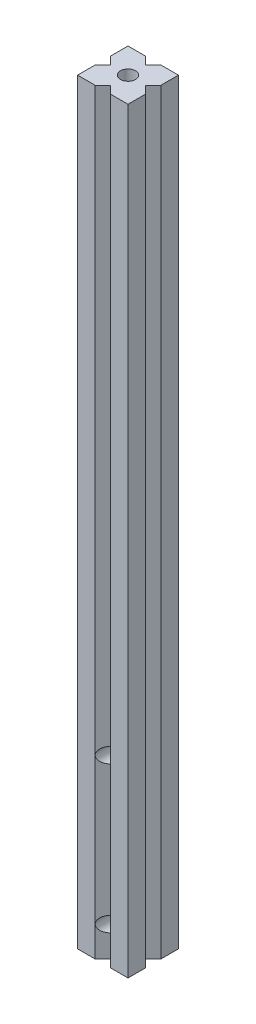
SolidWorks part; units mm, degrees
ref_plane "Front" through (0, 0, 0) normal (0, 0, 1) x (1, 0, 0)
ref_plane "Top" through (0, 0, 0) normal (0, 1, 0) x (1, 0, 0)
ref_plane "Right" through (0, 0, 0) normal (1, 0, 0) x (0, 0, -1)
sketch "Skizze1" plane through (0, 0, 0) normal (0, 1, 0) x (1, 0, 0)
  line L1 (0, 0) -> (20, 0)
  line L2 (0, 0) -> (0, 20)
  line L3 (0, 20) -> (20, 20)
  line L4 (20, 0) -> (20, 20)
  dimension "D1" = 20
extrude "Aufsatz-Linear austragen1" add sketch "Skizze1" along normal blind 300
sketch "Skizze2" plane through (0, 300, 0) normal (0, 1, 0) x (1, 0, 0)
  line L0 (10, 20) -> (10, 0) construction
  line L1 (0, 10) -> (20, 10) construction
  line L2 (7, 20) -> (10, 17)
  line L3 (13, 20) -> (10, 17)
  line L4 (10, 10) -> (20, 20) construction
  line L5 (7, 20) -> (13, 20)
  line L6 (20, 13) -> (17, 10)
  line L7 (20, 7) -> (17, 10)
  line L8 (20, 7) -> (20, 13)
  line L9 (0, 7) -> (0, 13)
  line L10 (0, 7) -> (3, 10)
  line L11 (0, 13) -> (3, 10)
  line L12 (7, 0) -> (13, 0)
  line L13 (13, 0) -> (10, 3)
  line L14 (7, 0) -> (10, 3)
  line L15 (20, 20) -> (0, 20) construction
  line L16 (20, 0) -> (20, 20) construction
  line L17 (0, 0) -> (20, 0) construction
  dimension "D1" = 3
  dimension "D2" = 3
extrude "Schnitt-Linear austragen1" cut sketch "Skizze2" against normal through all
ref_plane "Ebene1" through (10, 0, 0) normal (1, 0, 0) x (0, 0, -1)
sketch "Skizze3" plane through (0, 300, 0) normal (0, 1, 0) x (1, 0, 0)
  line L0 (3, 10) -> (17, 10) construction
  circle A0 centre (10, 10) radius 3
  dimension "D1" = 6
extrude "Schnitt-Linear austragen2" cut sketch "Skizze3" against normal through all
ref_plane "Plane1" through (0, 150, 0) normal (0, 1, 0) x (1, 0, 0)
ref_plane "Plane2" through (0, 0, -10) normal (0, 0, -1) x (-1, 0, 0)
sketch "Sketch1" plane through (0, 0, 0) normal (0, 0, 1) x (1, 0, 0)
  line L0 (10, 0) -> (10, 300) construction
  line L1 (13, 0) -> (20, 0) construction
  circle A0 centre (10, 12) radius 3
  circle A1 centre (10, 70) radius 3
  dimension "D1" = 6
  dimension "D3" = 70
  dimension "D2" = 12
extrude "Cut-Extrude1" cut sketch "Sketch1" against normal through all
